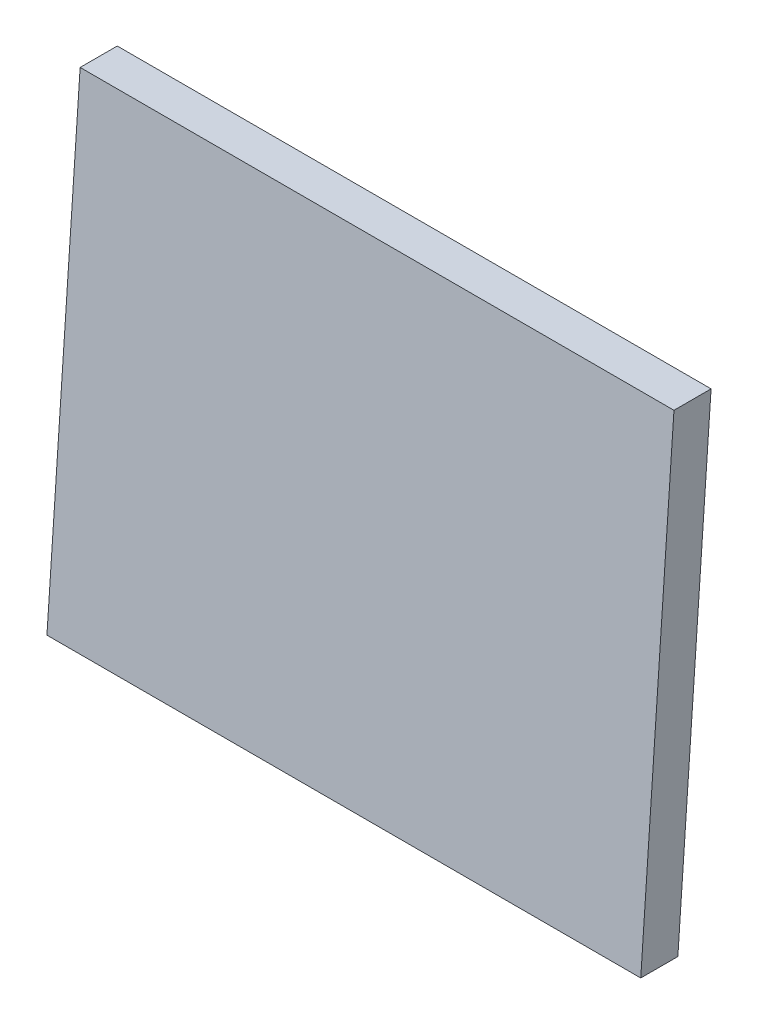
SolidWorks part; units mm, degrees
other "Markup1"
sketch "Sketch2" plane through (0, 320, -22.3766) normal (-0.79, 0.322, -0.5217) x (-0.5064, 0.1369, 0.8514)
ref_plane "Front Plane" through (0, 0, 0) normal (0, 0, 1) x (1, 0, 0)
ref_plane "Top Plane" through (0, 0, 0) normal (0, 1, 0) x (1, 0, 0)
ref_plane "Right Plane" through (0, 0, 0) normal (1, 0, 0) x (0, 0, -1)
sketch "Sketch1" plane through (0, 0, 0) normal (1, 0, 0) x (0, 0, -1)
  line L0 (-25, 0) -> (0, 0)
  line L1 (0, 0) -> (22.3766, 320)
  line L2 (22.3766, 320) -> (-2.6234, 320)
  line L3 (-2.6234, 320) -> (-25, 0)
  dimension "D1" = 94
  dimension "D2" = 86
  dimension "D3" = 25
  dimension "D4" = 320
extrude "Boss-Extrude1" add sketch "Sketch1" along normal blind 400 contours L3 L0 L1 L2
